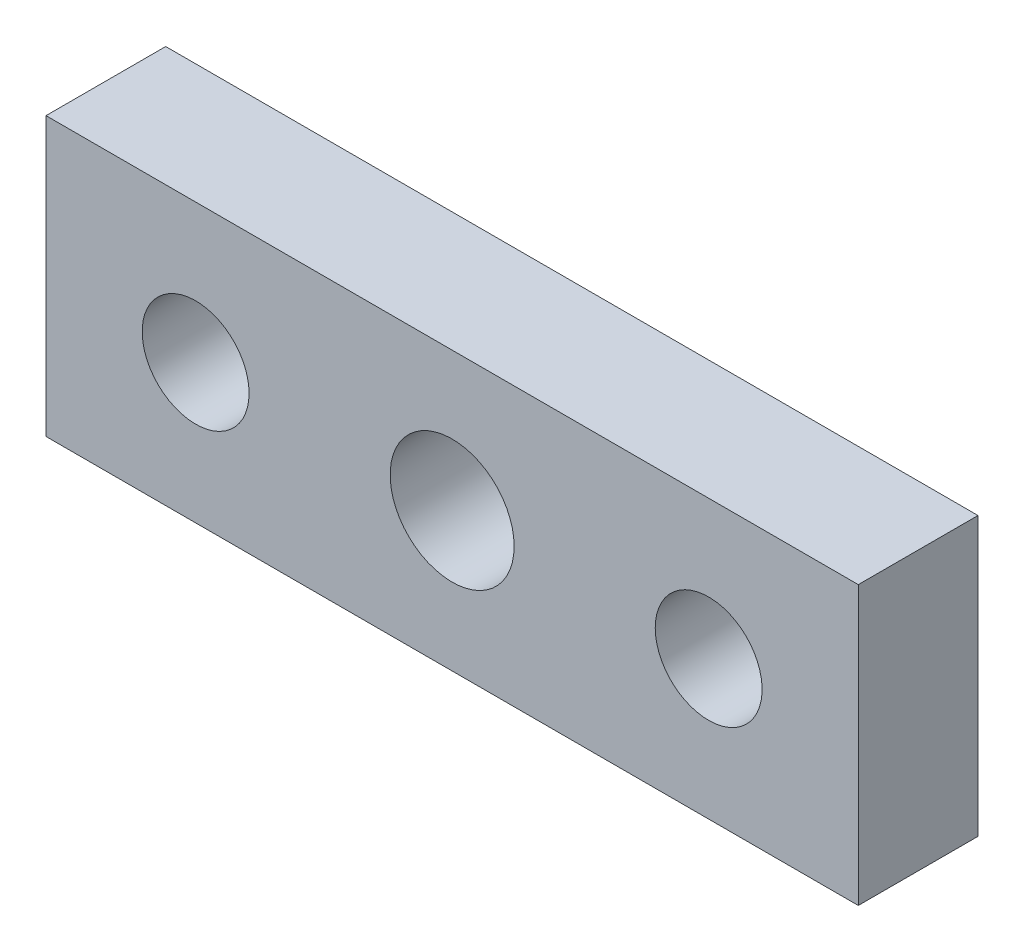
SolidWorks part; units mm, degrees
ref_plane "Front" through (0, 0, 0) normal (0, 0, 1) x (1, 0, 0)
ref_plane "Top" through (0, 0, 0) normal (0, 1, 0) x (1, 0, 0)
ref_plane "Right" through (0, 0, 0) normal (1, 0, 0) x (0, 0, -1)
sketch "Sketch1" plane through (0, 0, 0) normal (0, 0, 1) x (1, 0, 0)
  line L0 (0, 0) -> (-19, 0) construction
  line L1 (-19, -6.5) -> (19, -6.5)
  line L2 (-19, -6.5) -> (-19, 6.5)
  line L3 (-19, 6.5) -> (19, 6.5)
  line L4 (19, -6.5) -> (19, 6.5)
  line L5 (-19, -6.5) -> (19, 6.5) construction
  line L6 (-19, 6.5) -> (19, -6.5) construction
  line L7 (0, 6.5) -> (0, 0) construction
  circle A0 centre (0, 0) radius 2.9
  circle A1 centre (-12, 0) radius 2.5
  circle A2 centre (12, 0) radius 2.5
  point P0 (0, 0)
  dimension "D3" = 5.8
  dimension "D4" = 5
  dimension "D5" = 12
  dimension "D1" = 38
  dimension "D2" = 13
extrude "Boss-Extrude1" add sketch "Sketch1" along normal blind 5.6
